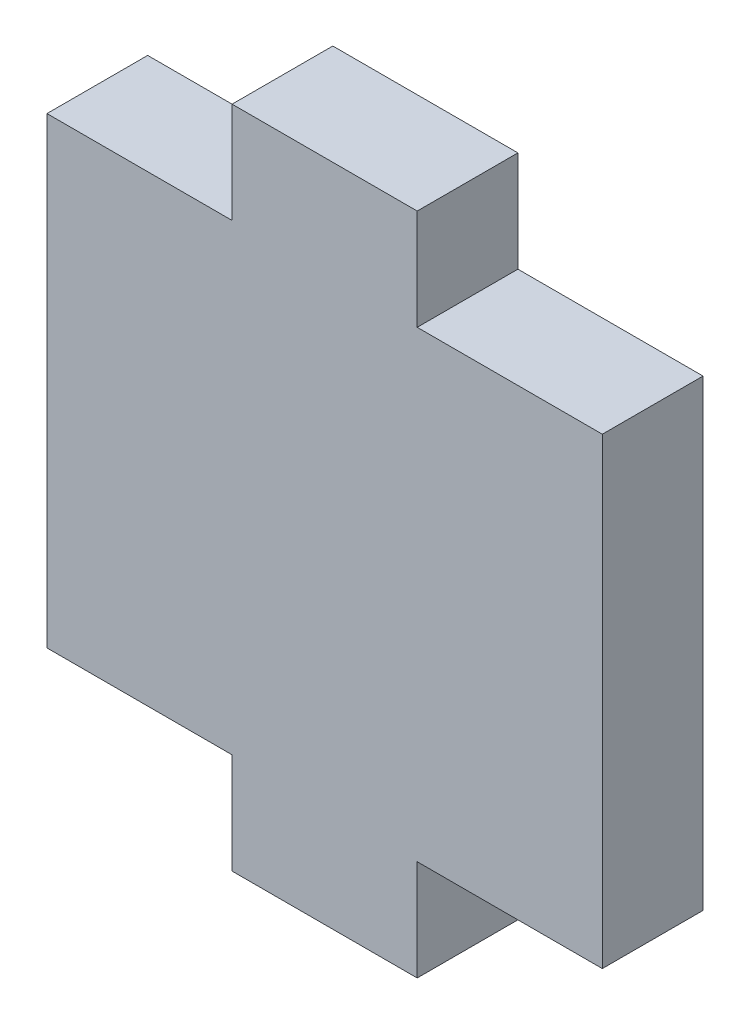
SolidWorks part; units mm, degrees
ref_plane "Front Plane" through (0, 0, 0) normal (0, 0, 1) x (1, 0, 0)
ref_plane "Top Plane" through (0, 0, 0) normal (0, 1, 0) x (1, 0, 0)
ref_plane "Right Plane" through (0, 0, 0) normal (1, 0, 0) x (0, 0, -1)
sketch "Sketch1" plane through (0, 0, 0) normal (0, 0, 1) x (1, 0, 0)
  line L0 (20, 0) -> (30, 0)
  line L1 (0, 0) -> (10, 0)
  line L2 (0, 0) -> (0, 25)
  line L3 (10, 30.44) -> (20, 30.44)
  line L4 (30, 0) -> (30, 25)
  line L7 (0, 25) -> (10, 25)
  line L8 (10, 30.44) -> (10, 25)
  line L11 (30, 25) -> (20, 25)
  line L12 (20, 30.44) -> (20, 25)
  line L14 (10, 0) -> (10, -5.44)
  line L15 (10, -5.44) -> (20, -5.44)
  line L16 (20, 0) -> (20, -5.44)
  dimension "D1" = 30.44
  dimension "D2" = 5.44
  dimension "D3" = 30
extrude "Boss-Extrude1" add sketch "Sketch1" along normal blind 5.44
equation "\"mat\"=\"mat@switch box.assembly\""
equation "\"D1@Sketch1\"=25+\"mat\""
equation "\"D2@Sketch1\" = \"mat\""
equation "\"D1@Boss-Extrude1\"=\"mat\""
